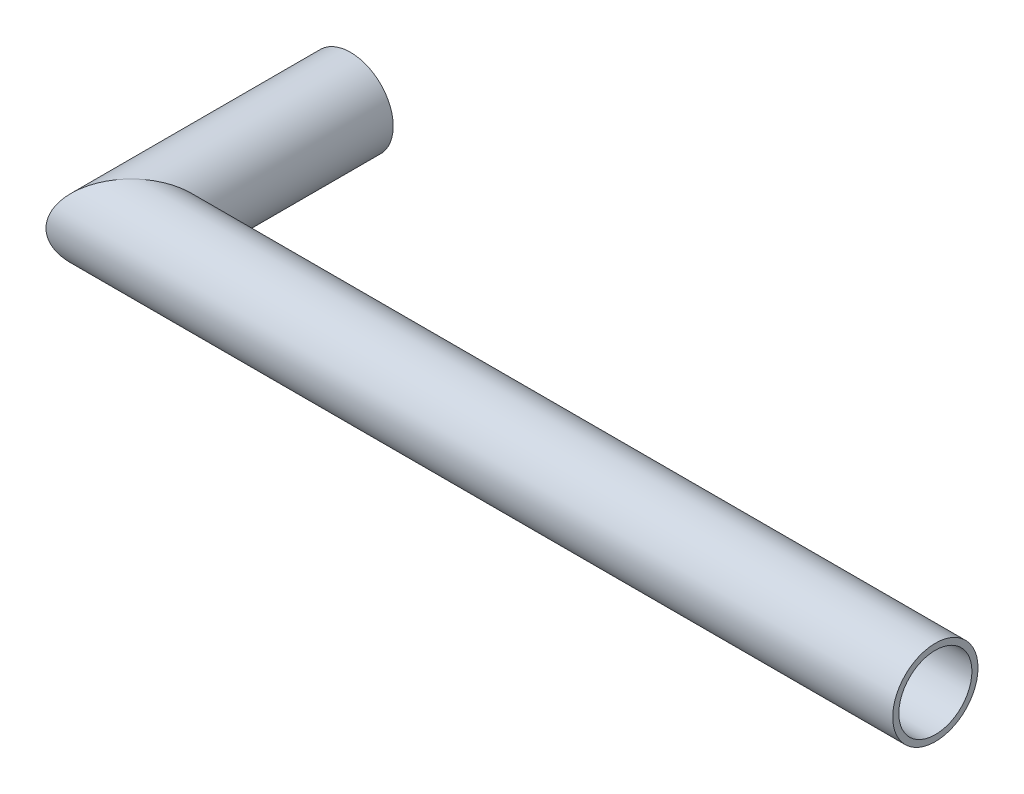
SolidWorks part; units mm, degrees
ref_plane "Front Plane" through (0, 0, 0) normal (0, 0, 1) x (1, 0, 0)
ref_plane "Top Plane" through (0, 0, 0) normal (0, 1, 0) x (1, 0, 0)
ref_plane "Right Plane" through (0, 0, 0) normal (1, 0, 0) x (0, 0, -1)
sketch "Sketch1" plane through (0, 0, 0) normal (0, 1, 0) x (1, 0, 0)
  line L0 (0, 180) -> (0, 0)
  line L1 (0, 0) -> (660, 0)
  dimension "D1" = 660
  dimension "D2" = 180
ref_plane "Plane1" through (0, 0, -180) normal (0, 0, 1) x (1, 0, 0)
sketch "Sketch2" plane through (0, 0, -180) normal (0, 0, 1) x (1, 0, 0)
  circle A0 centre (0, 0) radius 30
  dimension "D1" = 60
sweep "Sweep-Thin1" add profiles "Sketch2" path "Sketch1" parameters "D1"=5
